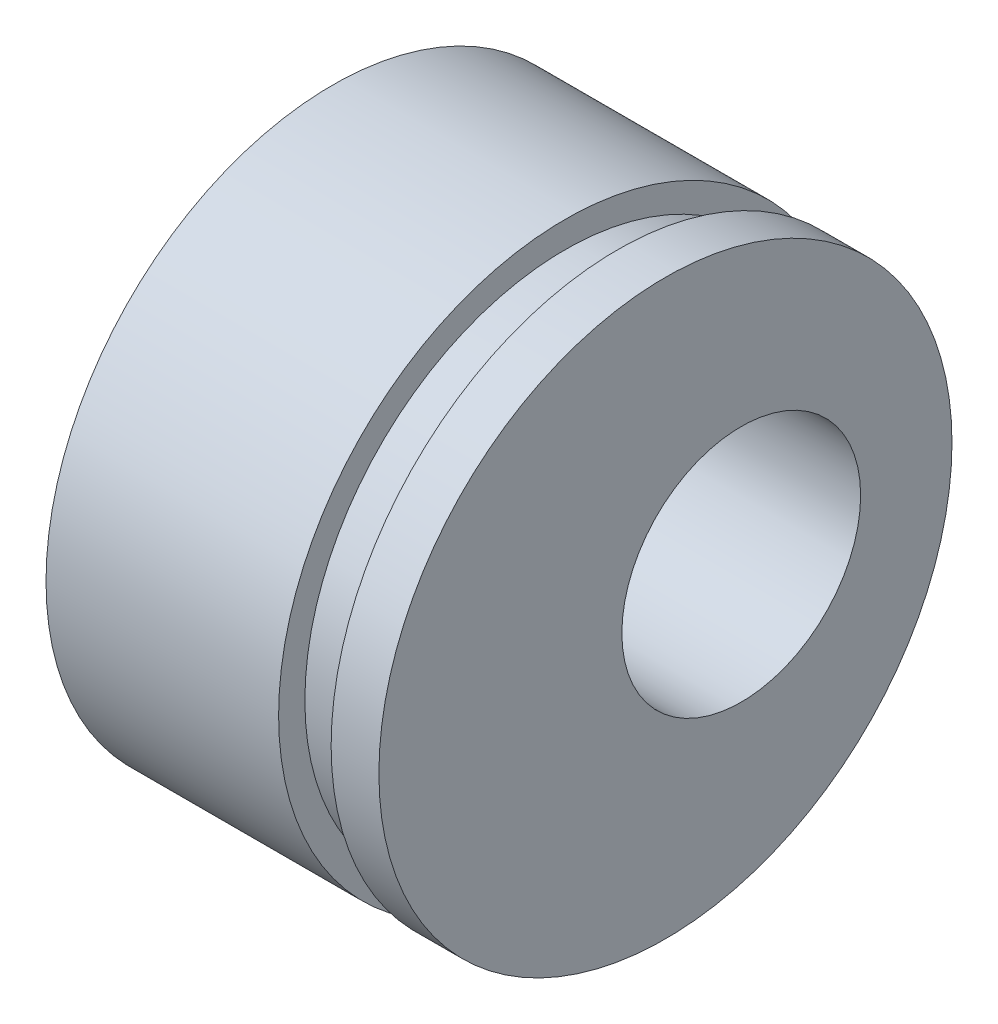
SolidWorks part; units mm, degrees
ref_plane "Front Plane" through (0, 0, 0) normal (0, 0, 1) x (1, 0, 0)
ref_plane "Top Plane" through (0, 0, 0) normal (0, 1, 0) x (1, 0, 0)
ref_plane "Right Plane" through (0, 0, 0) normal (1, 0, 0) x (0, 0, -1)
sketch "Sketch2" plane through (0, 0, 0) normal (0, 0, 1) x (1, 0, 0)
  line L0 (0, 0) -> (58.591, 0) construction
  line L2 (0, 0) -> (18.4, 0)
  line L3 (0, 0) -> (0, 2.5)
  line L4 (0, 2.5) -> (18.4, 2.5)
  line L5 (18.4, 0) -> (18.4, 2.5)
  line L6 (6.0094, 2.5) -> (6.0094, 6)
  line L11 (6.0094, 6) -> (9.9794, 6)
  line L16 (12.9794, 6) -> (12.9794, 3)
  line L17 (12.9794, 3) -> (13.6398, 3)
  line L18 (13.6398, 3) -> (13.6398, 2.5)
  line L19 (13.6398, 2.5) -> (6.0094, 2.5)
  line L22 (13.6398, 2.5) -> (16.1198, 2.5)
  line L23 (13.6398, 2.5) -> (13.6398, 4)
  line L24 (13.6398, 4) -> (16.1198, 4)
  line L25 (16.1198, 2.5) -> (16.1198, 4)
  line L27 (6.0094, 6) -> (9.9794, 6)
  line L28 (6.0094, 6) -> (6.0094, 9)
  line L29 (6.0094, 9) -> (9.9794, 9)
  line L30 (9.9794, 6) -> (9.9794, 9)
  line L31 (6.0094, 9) -> (6.0094, 8.25)
  line L32 (6.0094, 8.25) -> (5.0094, 8.25)
  line L33 (8.6609, 22.001) -> (8.6609, 12.476) construction
  line L34 (5.0094, 12.476) -> (12.3124, 12.476)
  line L35 (9.9794, 9) -> (12.3124, 9)
  line L36 (5.0094, 7.9375) -> (1.7709, 7.9375)
  line L37 (5.0094, 8.25) -> (5.0094, 12.476)
  line L38 (5.0094, 7.9375) -> (5.0094, 13.9365)
  line L39 (5.0094, 13.9365) -> (1.7709, 13.9365)
  line L40 (1.7709, 7.9375) -> (1.7709, 13.9365)
  line L41 (5.0094, 22.001) -> (12.3124, 22.001)
  line L42 (5.0094, 22.001) -> (5.0094, 30.1625)
  line L43 (5.0094, 30.1625) -> (12.3124, 30.1625)
  line L44 (12.3124, 22.001) -> (12.3124, 30.1625)
  line L49 (16.6398, 22.001) -> (16.6398, 7.5)
  line L51 (23.0198, 7.5) -> (23.0198, 6.5)
  line L54 (16.1198, 4) -> (13.6398, 4)
  line L56 (18.0398, 7.5) -> (23.0198, 7.5)
  line L57 (13.3124, 22.001) -> (16.6398, 22.001)
  line L58 (16.1198, 3.5) -> (20.0198, 3.5)
  line L59 (29.9098, 14) -> (26.9098, 11)
  line L60 (4.0094, 31.75) -> (18.0398, 31.75)
  line L61 (18.0398, 7.5) -> (23.0198, 7.5)
  line L62 (18.0398, 7.5) -> (18.0398, 12)
  line L63 (18.0398, 12) -> (23.0198, 12)
  line L64 (23.0198, 7.5) -> (23.0198, 12)
  line L65 (18.0398, 31.75) -> (18.0398, 12)
  line L66 (23.0198, 11) -> (26.9098, 11)
  line L67 (34.8098, 23) -> (31.3098, 19.5)
  line L68 (35.8098, 31) -> (38.7998, 33.99)
  line L69 (29.9098, 14) -> (29.9098, 15)
  line L70 (29.9098, 15) -> (22.9398, 15)
  line L71 (22.9398, 15) -> (21.0398, 15)
  line L72 (18.0398, 7.5) -> (16.6398, 7.5)
  line L73 (21.0398, 15) -> (21.0398, 43)
  line L74 (19.6115, 40) -> (9.6516, 40)
  line L75 (9.6516, 40) -> (4.0094, 40)
  line L76 (21.0398, 43) -> (19.6115, 43)
  line L77 (22.9398, 15) -> (29.9098, 15)
  line L78 (22.9398, 15) -> (22.9398, 21)
  line L79 (22.9398, 21) -> (29.9098, 21)
  line L80 (29.9098, 15) -> (29.9098, 21)
  line L81 (9.6516, 40) -> (19.6115, 40)
  line L82 (9.6516, 40) -> (9.6516, 50)
  line L83 (9.6516, 50) -> (19.6115, 50)
  line L84 (19.6115, 40) -> (19.6115, 50)
  line L85 (4.0094, 40) -> (4.0094, 31.75)
  line L86 (12.9794, 3) -> (12.9794, 2.5)
  line L87 (31.3098, 19.5) -> (29.9098, 19.5)
  line L88 (21.4694, 63.5) -> (21.4694, 51.308)
  line L89 (21.4694, 63.5) -> (25.9398, 63.5)
  line L90 (25.9398, 63.5) -> (25.9398, 25)
  line L91 (27.8398, 25) -> (25.9398, 25)
  line L92 (9.6516, 48) -> (8.2233, 48)
  line L93 (8.2233, 48) -> (8.2233, 53.476)
  line L94 (8.2233, 53.476) -> (19.6115, 53.476)
  line L95 (19.6115, 53.476) -> (19.6115, 50)
  line L96 (13.9174, 63.001) -> (13.9174, 53.476) construction
  line L97 (8.2233, 63.001) -> (19.6115, 63.001)
  line L98 (8.2233, 63.001) -> (8.2233, 68.2625)
  line L99 (8.2233, 68.2625) -> (19.6115, 68.2625)
  line L100 (19.6115, 63.001) -> (19.6115, 68.2625)
  line L101 (12.9794, 6) -> (11.9794, 6)
  line L102 (8.2233, 44.825) -> (4.9848, 44.825)
  line L103 (8.2233, 44.825) -> (8.2233, 54.9365)
  line L104 (8.2233, 54.9365) -> (4.9848, 54.9365)
  line L106 (9.9794, 6) -> (10.8794, 6)
  line L107 (27.8398, 25) -> (34.8098, 25)
  line L108 (34.8098, 25) -> (34.8098, 23)
  line L109 (0, 0) -> (-2, 0)
  line L110 (0, 0) -> (0, 11)
  line L111 (27.8398, 25) -> (34.8098, 25)
  line L112 (27.8398, 25) -> (27.8398, 32.5)
  line L113 (27.8398, 32.5) -> (34.8098, 32.5)
  line L114 (34.8098, 25) -> (34.8098, 32.5)
  line L115 (35.8098, 31) -> (34.8098, 31)
  line L116 (27.8398, 32.5) -> (27.8398, 64.5)
  line L117 (20.5849, 74.025) -> (6.2499, 74.025)
  line L118 (6.2499, 74.025) -> (6.2499, 76.2)
  line L119 (38.7998, 47.29) -> (30.8398, 55.25)
  line L120 (0, 11) -> (-2, 11)
  line L121 (38.7998, 43.815) -> (30.8623, 43.815)
  line L123 (-4.8152, 69.85) -> (1.5348, 76.2)
  line L124 (38.7998, 47.29) -> (38.7998, 33.99)
  line L125 (-2, 0) -> (-2, 11)
  line L126 (38.7998, 37.465) -> (30.8623, 37.465)
  line L127 (30.8623, 43.815) -> (30.8623, 37.465)
  line L128 (6.0094, 2.5) -> (6.0094, 0)
  line L129 (-0.0152, 63.5) -> (-0.0152, 30)
  line L132 (4.9848, 63.5) -> (-0.0152, 63.5)
  line L136 (-1.8152, 30) -> (-11.7752, 30)
  line L138 (-13.7752, 25.4) -> (-2, 25.4)
  line L139 (-2, 25.4) -> (-2, 11.5)
  line L140 (27.8398, 64.5) -> (20.5849, 64.5)
  line L141 (-1.8152, 30) -> (-11.7752, 30)
  line L142 (-1.8152, 30) -> (-1.8152, 39)
  line L143 (-1.8152, 39) -> (-11.7752, 39)
  line L144 (-11.7752, 30) -> (-11.7752, 39)
  line L145 (20.5849, 64.5) -> (20.5849, 74.025)
  line L146 (-12.7752, 37) -> (-12.7752, 47.29)
  line L147 (-12.7752, 37) -> (-11.7752, 37)
  line L148 (30.8398, 55.25) -> (30.8398, 76.2)
  line L149 (11.9794, 6) -> (11.9794, 5.45)
  line L154 (-2, 11.5) -> (0.5, 11.5)
  line L155 (4.9848, 60.6197) -> (24.0348, 60.6197)
  line L160 (4.9848, 60.6197) -> (4.9848, 55.8572)
  line L161 (4.9848, 55.8572) -> (24.0348, 55.8572)
  line L166 (24.0348, 60.6197) -> (24.0348, 55.8572)
  line L167 (4.9848, 60.6197) -> (24.0348, 55.8572) construction
  line L172 (4.9848, 55.8572) -> (24.0348, 60.6197) construction
  line L173 (24.0348, 62.2072) -> (25.9398, 62.2072)
  line L174 (11.9794, 5.45) -> (10.8794, 5.45)
  line L175 (10.8794, 6) -> (10.8794, 5.45)
  line L176 (24.0348, 62.2072) -> (24.0348, 54.2697)
  line L177 (24.0348, 54.2697) -> (25.9398, 54.2697)
  line L178 (25.9398, 62.2072) -> (25.9398, 54.2697)
  line L179 (24.0348, 62.2072) -> (25.9398, 54.2697) construction
  line L180 (24.0348, 54.2697) -> (25.9398, 62.2072) construction
  line L181 (3, 19.6197) -> (15.7, 19.6197)
  line L182 (3, 19.6197) -> (3, 14.8572)
  line L183 (3, 14.8572) -> (15.7, 14.8572)
  line L184 (15.7, 19.6197) -> (15.7, 14.8572)
  line L185 (3, 19.6197) -> (15.7, 14.8572) construction
  line L186 (3, 14.8572) -> (15.7, 19.6197) construction
  line L187 (15.7, 21.2072) -> (16.6398, 21.2072)
  line L188 (15.7, 21.2072) -> (15.7, 13.2697)
  line L189 (15.7, 13.2697) -> (16.6398, 13.2697)
  line L190 (16.6398, 21.2072) -> (16.6398, 13.2697)
  line L191 (15.7, 21.2072) -> (16.6398, 13.2697) construction
  line L192 (15.7, 13.2697) -> (16.6398, 21.2072) construction
  line L193 (0.5, 11.5) -> (0.5, 6.9375)
  line L194 (0.5, 6.9375) -> (1.7709, 6.9375)
  line L195 (23.0198, 6.5) -> (20.0198, 3.5)
  line L196 (4.9848, 63.5) -> (4.9848, 54.9365)
  line L197 (3, 43.825) -> (4.9848, 43.825)
  line L198 (1.7709, 6.9375) -> (1.7709, 7.9375)
  line L199 (6.0094, 0) -> (12.9794, 0)
  line L200 (12.9794, 0) -> (12.9794, 2.5)
  line L201 (18.0398, 31.75) -> (18.0398, 35.875)
  line L202 (18.0398, 35.875) -> (21.0398, 35.875)
  line L203 (30.8398, 76.2) -> (6.2499, 76.2)
  line L204 (2.8049, 69.85) -> (7.2499, 69.85) construction
  line L205 (7.2499, 67.4688) -> (26.2999, 67.4688)
  line L206 (7.2499, 74.025) -> (7.2499, 64.5)
  line L207 (7.2499, 64.5) -> (-1.8152, 64.5)
  line L208 (-1.8152, 64.5) -> (-1.8152, 39)
  line L209 (-12.7752, 47.29) -> (-4.8152, 55.25)
  line L210 (-4.8152, 55.25) -> (-4.8152, 69.85)
  line L211 (7.2499, 67.4688) -> (7.2499, 72.2312)
  line L212 (7.2499, 72.2312) -> (26.2999, 72.2313)
  line L213 (26.2999, 67.4688) -> (26.2999, 72.2313)
  line L214 (26.2999, 73.8187) -> (30.8398, 73.8187)
  line L215 (26.2999, 73.8187) -> (26.2999, 65.8813)
  line L216 (26.2999, 65.8813) -> (30.8398, 65.8813)
  line L217 (30.8398, 73.8187) -> (30.8398, 65.8813)
  line L218 (2.8049, 72.2313) -> (25.0299, 72.2313)
  line L219 (2.8049, 72.2313) -> (2.8049, 67.4687)
  line L220 (2.8049, 67.4687) -> (25.0299, 67.4687)
  line L221 (25.0299, 72.2313) -> (25.0299, 67.4687)
  line L222 (25.0299, 69.85) -> (20.5849, 69.85) construction
  line L223 (21.4694, 51.308) -> (22.9398, 51.308)
  line L224 (22.9398, 51.308) -> (22.9398, 21)
  line L225 (13.6398, 4) -> (13.6398, 12.2697)
  line L226 (13.6398, 12.2697) -> (13.3124, 12.2697)
  line L227 (13.3124, 12.2697) -> (13.3124, 22.001)
  line L228 (12.3124, 9) -> (12.3124, 12.476)
  line L229 (-1.8152, 30) -> (-0.0152, 30)
  line L230 (8.2233, 65.6317) -> (2.8049, 65.6317) construction
  line L231 (19.6115, 65.6317) -> (25.0299, 65.6317) construction
  line L232 (1.5348, 76.2) -> (6.2499, 76.2)
  line L233 (-11.7752, 30) -> (-13.7752, 30)
  line L234 (-13.7752, 30) -> (-13.7752, 25.4)
  line L235 (3, 13.9365) -> (3, 43.825)
  line L236 (4.9848, 54.9365) -> (4.9848, 44.825)
  line L237 (4.9848, 43.825) -> (4.9848, 44.825)
  circle A0 centre (26.8898, 25.95) radius 0.95
  circle A1 centre (21.9898, 15.95) radius 0.95
  circle A2 centre (17.3398, 8.2) radius 0.7
  circle A3 centre (10.4294, 6.45) radius 0.45
  circle A4 centre (-0.9152, 30.9) radius 0.9
  point P7 (24.9873, 58.2385)
  point P131 (16.1699, 17.2385)
  point P135 (14.5098, 58.2385)
  point P146 (9.35, 17.2385)
sketch "Sketch3" plane through (0, 0, 0) normal (0, 0, 1) x (1, 0, 0)
  line L0 (12.9794, 3) -> (12.9794, 2.5) construction
  line L1 (11.9794, 6) -> (11.9794, 5.45) construction
  line L2 (12.9794, 6) -> (11.9794, 6) construction
  line L3 (12.9794, 6) -> (12.9794, 3) construction
  line L5 (10.8794, 6) -> (10.8794, 5.45) construction
  line L6 (11.9794, 5.45) -> (10.8794, 5.45) construction
  line L7 (6.0094, 2.5) -> (6.0094, 6) construction
  line L8 (6.0094, 6) -> (9.9794, 6) construction
  line L9 (9.9794, 6) -> (10.8794, 6) construction
  line L10 (12.9794, 3) -> (12.9794, 2.5)
  line L11 (11.9794, 6) -> (11.9794, 5.45)
  line L12 (12.9794, 6) -> (11.9794, 6)
  line L13 (12.9794, 6) -> (12.9794, 3)
  line L15 (10.8794, 6) -> (10.8794, 5.45)
  line L16 (11.9794, 5.45) -> (10.8794, 5.45)
  line L17 (6.0094, 2.5) -> (6.0094, 6)
  line L18 (6.0094, 6) -> (9.9794, 6)
  line L19 (9.9794, 6) -> (10.8794, 6)
  line L20 (6.0094, 2.5) -> (6.0094, 0) construction
  line L21 (0, 0) -> (18.4, 0) construction
  line L22 (12.9794, 0) -> (12.9794, 2.5) construction
  line L23 (6.0094, 2.5) -> (6.0094, 0)
  line L24 (6.0094, 0) -> (12.9794, 0)
  line L25 (12.9794, 0) -> (12.9794, 2.5)
revolve "Revolve1" add sketch "Sketch3" angle 360 about L24
sketch "Sketch4" plane through (0, 0, 0) normal (1, 0, 0) x (0, 0, -1)
  line L0 (0, 0) -> (0, 69.85) construction
  line L1 (0, 0) -> (13.6271, 68.5079) construction
  line L2 (0, 0) -> (0, 58.2385) construction
  line L3 (0, 0) -> (50.436, 29.1192) construction
  line L4 (0, 0) -> (0, 31.75) construction
  line L5 (0, 0) -> (12.1502, 29.3332) construction
  line L6 (0, 0) -> (0, 17.2385) construction
  line L7 (0, 0) -> (14.929, 8.6192) construction
  line L8 (0, 0) -> (0, 58.2385) construction
  line L9 (0, 0) -> (50.436, 29.1192) construction
  line L10 (0, 0) -> (5.9583, 29.9542) construction
  line L11 (0, 0) -> (16.9677, 25.394) construction
  circle A0 centre (0, 0) radius 69.85 construction
  circle A1 centre (0, 0) radius 58.2385 construction
  circle A2 centre (0, 0) radius 31.75 construction
  circle A3 centre (0, 0) radius 17.2385 construction
  circle A4 centre (0, 69.85) radius 3.175
  circle A5 centre (0, 58.2385) radius 4.7625
  circle A6 centre (0, 31.75) radius 3.175
  circle A7 centre (0, 17.2385) radius 4.7625
  circle A8 centre (13.6271, 68.5079) radius 3.175
  circle A9 centre (26.7304, 64.533) radius 3.175
  circle A10 centre (38.8066, 58.0782) radius 3.175
  circle A11 centre (49.3914, 49.3914) radius 3.175
  circle A12 centre (58.0782, 38.8066) radius 3.175
  circle A13 centre (64.533, 26.7304) radius 3.175
  circle A14 centre (68.5079, 13.6271) radius 3.175
  circle A15 centre (69.85, 0) radius 3.175
  circle A16 centre (68.5079, -13.6271) radius 3.175
  circle A17 centre (64.533, -26.7304) radius 3.175
  circle A18 centre (58.0782, -38.8066) radius 3.175
  circle A19 centre (49.3914, -49.3914) radius 3.175
  circle A20 centre (38.8066, -58.0782) radius 3.175
  circle A21 centre (26.7304, -64.533) radius 3.175
  circle A22 centre (13.6271, -68.5079) radius 3.175
  circle A23 centre (0, -69.85) radius 3.175
  circle A24 centre (-13.6271, -68.5079) radius 3.175
  circle A25 centre (-26.7304, -64.533) radius 3.175
  circle A26 centre (-38.8066, -58.0782) radius 3.175
  circle A27 centre (-49.3914, -49.3914) radius 3.175
  circle A28 centre (-58.0782, -38.8066) radius 3.175
  circle A29 centre (-64.533, -26.7304) radius 3.175
  circle A30 centre (-68.5079, -13.6271) radius 3.175
  circle A31 centre (-69.85, 0) radius 3.175
  circle A32 centre (-68.5079, 13.6271) radius 3.175
  circle A33 centre (-64.533, 26.7304) radius 3.175
  circle A34 centre (-58.0782, 38.8066) radius 3.175
  circle A35 centre (-49.3914, 49.3914) radius 3.175
  circle A36 centre (-38.8066, 58.0782) radius 3.175
  circle A37 centre (-26.7304, 64.533) radius 3.175
  circle A38 centre (-13.6271, 68.5079) radius 3.175
  circle A47 centre (50.436, 29.1192) radius 4.7625
  circle A48 centre (50.436, -29.1192) radius 4.7625
  circle A49 centre (0, -58.2385) radius 4.7625
  circle A50 centre (-50.436, -29.1192) radius 4.7625
  circle A51 centre (-50.436, 29.1192) radius 4.7625
  circle A58 centre (12.1502, 29.3332) radius 3.175
  circle A59 centre (22.4506, 22.4506) radius 3.175
  circle A60 centre (29.3332, 12.1502) radius 3.175
  circle A61 centre (31.75, 0) radius 3.175
  circle A62 centre (29.3332, -12.1502) radius 3.175
  circle A63 centre (22.4506, -22.4506) radius 3.175
  circle A64 centre (12.1502, -29.3332) radius 3.175
  circle A65 centre (0, -31.75) radius 3.175
  circle A66 centre (-12.1502, -29.3332) radius 3.175
  circle A67 centre (-22.4506, -22.4506) radius 3.175
  circle A68 centre (-29.3332, -12.1502) radius 3.175
  circle A69 centre (-31.75, 0) radius 3.175
  circle A70 centre (-29.3332, 12.1502) radius 3.175
  circle A71 centre (-22.4506, 22.4506) radius 3.175
  circle A72 centre (14.929, 8.6192) radius 4.7625
  circle A73 centre (14.929, -8.6192) radius 4.7625
  circle A74 centre (0, -17.2385) radius 4.7625
  circle A75 centre (-14.929, -8.6192) radius 4.7625
  circle A76 centre (-14.929, 8.6192) radius 4.7625
  circle A77 centre (0, 0) radius 50
  circle A78 centre (0, 0) radius 9
  circle A79 centre (-12.1502, 29.3332) radius 3.175
  circle A80 centre (0, 0) radius 76.2
  circle A81 centre (0, 0) radius 74.025
  circle A82 centre (0, 69.85) radius 3.9687
  circle A83 centre (49.3914, 49.3914) radius 3.9687
  circle A84 centre (69.85, 0) radius 3.9688
  circle A85 centre (49.3914, -49.3914) radius 3.9687
  circle A86 centre (0, -69.85) radius 3.9687
  circle A87 centre (-49.3914, -49.3914) radius 3.9687
  circle A88 centre (-69.85, 0) radius 3.9688
  circle A89 centre (-49.3914, 49.3914) radius 3.9687
  circle A90 centre (0, 69.85) radius 2.3812
  circle A91 centre (13.6271, 68.5079) radius 2.3812
  circle A92 centre (26.7304, 64.533) radius 2.3813
  circle A93 centre (38.8066, 58.0782) radius 2.3812
  circle A94 centre (49.3914, 49.3914) radius 2.3812
  circle A95 centre (58.0782, 38.8066) radius 2.3812
  circle A96 centre (64.533, 26.7304) radius 2.3813
  circle A97 centre (68.5079, 13.6271) radius 2.3813
  circle A98 centre (69.85, 0) radius 2.3813
  circle A99 centre (68.5079, -13.6271) radius 2.3813
  circle A100 centre (64.533, -26.7304) radius 2.3813
  circle A101 centre (58.0782, -38.8066) radius 2.3812
  circle A102 centre (49.3914, -49.3914) radius 2.3812
  circle A103 centre (38.8066, -58.0782) radius 2.3812
  circle A104 centre (26.7304, -64.533) radius 2.3813
  circle A105 centre (13.6271, -68.5079) radius 2.3812
  circle A106 centre (0, -69.85) radius 2.3812
  circle A107 centre (-13.6271, -68.5079) radius 2.3812
  circle A108 centre (-26.7304, -64.533) radius 2.3813
  circle A109 centre (-38.8066, -58.0782) radius 2.3812
  circle A110 centre (-49.3914, -49.3914) radius 2.3812
  circle A111 centre (-58.0782, -38.8066) radius 2.3812
  circle A112 centre (-64.533, -26.7304) radius 2.3812
  arc A113 (3.0399, 30.8338) -> (8.9911, 29.65) centre (5.9583, 29.9542) cw
  arc A114 (14.6081, 27.3234) -> (19.6532, 23.9523) centre (16.9677, 25.394) cw
  arc A115 (23.9523, 19.6532) -> (27.3234, 14.6081) centre (25.394, 16.9677) cw
  arc A116 (29.65, 8.9911) -> (30.8338, 3.0399) centre (29.9542, 5.9583) cw
  arc A117 (30.8338, -3.0399) -> (29.65, -8.9911) centre (29.9542, -5.9583) cw
  arc A118 (27.3234, -14.6081) -> (23.9523, -19.6532) centre (25.394, -16.9677) cw
  arc A119 (19.6532, -23.9523) -> (14.6081, -27.3234) centre (16.9677, -25.394) cw
  arc A120 (8.9911, -29.65) -> (3.0399, -30.8338) centre (5.9583, -29.9542) cw
  arc A121 (-3.0399, -30.8338) -> (-8.9911, -29.65) centre (-5.9583, -29.9542) cw
  arc A122 (-14.6081, -27.3234) -> (-19.6532, -23.9523) centre (-16.9677, -25.394) cw
  arc A123 (-23.9523, -19.6532) -> (-27.3234, -14.6081) centre (-25.394, -16.9677) cw
  arc A124 (-29.65, -8.9911) -> (-30.8338, -3.0399) centre (-29.9542, -5.9583) cw
  arc A125 (-30.8338, 3.0399) -> (-29.65, 8.9911) centre (-29.9542, 5.9583) cw
  arc A126 (-27.3234, 14.6081) -> (-23.9523, 19.6532) centre (-25.394, 16.9677) cw
  arc A127 (-19.6532, 23.9523) -> (-14.6081, 27.3234) centre (-16.9677, 25.394) cw
  arc A128 (-8.9911, 29.65) -> (-3.0399, 30.8338) centre (-5.9583, 29.9542) cw
  arc A129 (26.9875, 0) -> (26.9932, 0.1932) centre (30.2705, 0) cw
  arc A130 (65.0988, 0.2771) -> (65.0875, 0) centre (68.4964, 0) ccw
  circle A131 centre (1.5875, 0) radius 40
  circle A132 centre (1.5875, 0) radius 2.5
  circle A133 centre (1.5875, 0) radius 3
  circle A134 centre (1.5875, 0) radius 43
  circle A135 centre (-68.5079, -13.6271) radius 2.3813
  circle A136 centre (-69.85, 0) radius 2.3813
  circle A137 centre (-68.5079, 13.6271) radius 2.3813
  circle A138 centre (-64.533, 26.7304) radius 2.3812
  circle A139 centre (-58.0782, 38.8066) radius 2.3812
  circle A140 centre (-49.3914, 49.3914) radius 2.3812
  circle A141 centre (-38.8066, 58.0782) radius 2.3812
  circle A142 centre (-26.7304, 64.533) radius 2.3813
  circle A143 centre (-13.6271, 68.5079) radius 2.3812
  circle A144 centre (0, 58.2385) radius 2.3812
  circle A145 centre (0, 58.2385) radius 3.9688
  circle A146 centre (50.436, 29.1192) radius 3.9688
  circle A147 centre (50.436, 29.1192) radius 2.3813
  circle A148 centre (50.436, -29.1192) radius 3.9687
  circle A149 centre (50.436, -29.1192) radius 2.3812
  circle A150 centre (0, -58.2385) radius 3.9687
  circle A151 centre (0, -58.2385) radius 2.3812
  circle A152 centre (-50.436, -29.1192) radius 3.9687
  circle A153 centre (-50.436, -29.1192) radius 2.3812
  circle A154 centre (-50.436, 29.1192) radius 3.9687
  circle A155 centre (-50.436, 29.1192) radius 2.3812
  spline S1 degree 4 poles (26.9875, 0) (26.9875, -0.0248) (26.9882, -0.0743) (26.9912, -0.1613) (26.9992, -0.2849) (27.0142, -0.4323) (27.0403, -0.5994) (27.0821, -0.7965) (27.1455, -1.0177) (27.2241, -1.2336) (27.3173, -1.4437) (27.4329, -1.6623) (27.5739, -1.8864) (27.7427, -2.1125) (27.9417, -2.3365) (28.1305, -2.5184) (28.3007, -2.6647) (28.4457, -2.7828) (28.5617, -2.8775) (28.6745, -2.9758) (28.7813, -3.0807) (28.9057, -3.2206) (29.0482, -3.4108) (29.197, -3.6576) (29.3758, -4.0447) (29.5291, -4.5502) (29.6152, -5.1612) (29.5933, -5.8758) (29.4507, -6.5869) (29.186, -7.2733) (28.8461, -7.831) (28.4818, -8.2549) (28.1375, -8.5536) (27.8792, -8.7284) (27.6484, -8.8496) (27.4154, -8.9438) (27.2144, -9.0029) (27.0118, -9.0554) (26.7709, -9.1263) (26.5334, -9.2082) (26.2634, -9.3231) (25.9685, -9.4827) (25.5538, -9.7623) (25.0678, -10.2216) (24.6281, -10.8948) (24.3613, -11.7878) (24.3459, -12.6097) (24.4764, -13.2366) (24.6525, -13.7006) (24.8058, -14.0202) (24.9382, -14.271) (25.0503, -14.5321) (25.1258, -14.8064) (25.1736, -15.0995) (25.1911, -15.4094) (25.1742, -15.8163) (25.0891, -16.3148) (24.907, -16.8764) (24.5182, -17.6315) (23.9757, -18.2942) (23.3695, -18.7764) (22.7564, -19.084) (22.3641, -19.2199) (22.0554, -19.2923) (21.7533, -19.3289) (21.4612, -19.3296) (21.1723, -19.2896) (20.8852, -19.2417) (20.5956, -19.2104) (20.3043, -19.1994) (19.8669, -19.2177) (19.2899, -19.3231) (18.5833, -19.6092) (17.8444, -20.1834) (17.3807, -20.828) (17.1316, -21.424) (17.0182, -21.8879) (16.9714, -22.1971) (16.9537, -22.4701) (16.9533, -22.7044) (16.9619, -22.9384) (16.9737, -23.1333) (16.977, -23.3286) (16.9594, -23.5624) (16.9177, -23.8101) (16.834, -24.1055) (16.6578, -24.5276) (16.3623, -25.0151) (15.9278, -25.5198) (15.3432, -25.99) (14.6957, -26.3472) (14.0068, -26.5857) (13.3856, -26.6851) (12.847, -26.6849) (12.4166, -26.6224) (12.1324, -26.5468) (11.9058, -26.4598) (11.7342, -26.3753) (11.6017, -26.2989) (11.4727, -26.2169) (11.3444, -26.1337) (11.1825, -26.0322) (10.9836, -25.9179) (10.7435, -25.7991) (10.4587, -25.6867) (10.0106, -25.5536) (9.3843, -25.468) (8.599, -25.5363) (7.7243, -25.8773) (7.1093, -26.3459) (6.716, -26.8042) (6.4745, -27.1841) (6.3352, -27.4489) (6.215, -27.7227) (6.1113, -28.0028) (5.9959, -28.2789) (5.841, -28.5357) (5.6522, -28.7792) (5.4316, -29.007) (5.1188, -29.2711) (4.6965, -29.5439) (4.1624, -29.7882) (3.5487, -29.9564) (2.9521, -30.0296) (2.386, -30.0225) (1.8595, -29.949) (1.3409, -29.8055) (0.9058, -29.6147) (0.5544, -29.4004) (0.2828, -29.1832) (0.0847, -28.9875) (-0.0865, -28.768) (-0.2353, -28.5332) (-0.3904, -28.3016) (-0.5598, -28.0786) (-0.792, -27.8146) (-1.1036, -27.5274) (-1.5105, -27.2448) (-2.0688, -26.9834) (-2.7167, -26.8202) (-3.459, -26.7949) (-4.1529, -26.9407) (-4.7224, -27.1899) (-5.1296, -27.455) (-5.3866, -27.661) (-5.5925, -27.8507) (-5.7558, -28.014) (-5.9199, -28.1766) (-6.0977, -28.3246) (-6.3382, -28.4851) (-6.6906, -28.6628) (-7.1669, -28.8182) (-7.7668, -28.9076) (-8.4201, -28.8957) (-9.0747, -28.7804) (-9.7144, -28.5614) (-10.3217, -28.2381) (-10.8061, -27.8636) (-11.1671, -27.4837) (-11.4143, -27.1402) (-11.5734, -26.859) (-11.6946, -26.573) (-11.7735, -26.2857) (-11.8173, -25.9915) (-11.8668, -25.6988) (-11.9353, -25.4093) (-12.0257, -25.1261) (-12.198, -24.7091) (-12.5089, -24.187) (-13.0379, -23.6191) (-13.8448, -23.1355) (-14.6072, -22.9365) (-15.2369, -22.9149) (-15.701, -22.9694) (-16.0024, -23.0316) (-16.2609, -23.107) (-16.4782, -23.1841) (-16.6576, -23.2529) (-16.8015, -23.307) (-16.9839, -23.3672) (-17.2087, -23.4203) (-17.4853, -23.4534) (-17.811, -23.4543) (-18.2291, -23.4104) (-18.7305, -23.2885) (-19.2884, -23.06) (-19.8603, -22.7052) (-20.3581, -22.2764) (-20.7758, -21.7899) (-21.1086, -21.2598) (-21.3336, -20.7318) (-21.4619, -20.2263) (-21.5006, -19.8113) (-21.4889, -19.4989) (-21.4468, -19.2424) (-21.3965, -19.0408) (-21.34, -18.8332) (-21.2878, -18.6168) (-21.2341, -18.3322) (-21.1962, -17.9773) (-21.1985, -17.5604) (-21.2781, -17.0173) (-21.4721, -16.4256) (-21.838, -15.7861) (-22.3482, -15.2578) (-22.8946, -14.8957) (-23.3828, -14.6878) (-23.7368, -14.5834) (-24.0536, -14.5215) (-24.3285, -14.4876) (-24.6045, -14.47) (-24.8811, -14.458) (-25.1556, -14.4184) (-25.4228, -14.3439) (-25.6932, -14.2375) (-26.1109, -14.0218) (-26.5677, -13.6822) (-27.0258, -13.1981) (-27.4314, -12.5682) (-27.7017, -11.9578) (-27.8746, -11.3112) (-27.9332, -10.727) (-27.9111, -10.2247) (-27.8415, -9.8214) (-27.7568, -9.5159) (-27.6427, -9.2298) (-27.5004, -8.9659) (-27.3212, -8.7261) (-27.1301, -8.4966) (-26.9071, -8.1967) (-26.6417, -7.7583) (-26.3997, -7.1508) (-26.2841, -6.3875) (-26.3642, -5.5798) (-26.6019, -4.9055) (-26.9193, -4.3761) (-27.2736, -3.9636) (-27.583, -3.6904) (-27.8719, -3.4871) (-28.1186, -3.3407) (-28.3135, -3.2371) (-28.5043, -3.1411) (-28.6854, -3.0419) (-28.9002, -2.8984) (-29.1355, -2.6958) (-29.4123, -2.3882) (-29.6958, -1.9552) (-29.932, -1.437) (-30.0985, -0.839) (-30.1779, -0.2025) (-30.1603, 0.4599) (-30.0348, 1.1323) (-29.8199, 1.711) (-29.5617, 2.1719) (-29.3035, 2.5118) (-29.0784, 2.748) (-28.8655, 2.924) (-28.6761, 3.0468) (-28.5112, 3.1367) (-28.3775, 3.205) (-28.2106, 3.2911) (-28.0136, 3.4005) (-27.7912, 3.5413) (-27.5508, 3.7219) (-27.2011, 4.0343) (-26.7941, 4.5285) (-26.4419, 5.234) (-26.2777, 6.1494) (-26.351, 6.9081) (-26.5268, 7.4739) (-26.7218, 7.8823) (-26.8619, 8.1196) (-26.9953, 8.3144) (-27.1373, 8.5028) (-27.2613, 8.6553) (-27.3845, 8.8088) (-27.518, 9.0035) (-27.6324, 9.2103) (-27.7412, 9.4693) (-27.8326, 9.7814) (-27.9074, 10.1885) (-27.9345, 10.6913) (-27.8808, 11.2771) (-27.6878, 12.0229) (-27.3166, 12.8111) (-26.8405, 13.4278) (-26.3243, 13.8718) (-25.9118, 14.1263) (-25.6503, 14.2566) (-25.3769, 14.3596) (-25.0933, 14.4318) (-24.8027, 14.4634) (-24.5112, 14.4738) (-24.1629, 14.5033) (-23.7608, 14.5717) (-23.1887, 14.7443) (-22.5511, 15.0901) (-21.962, 15.6231) (-21.544, 16.2749) (-21.3217, 16.857) (-21.2175, 17.3851) (-21.1902, 17.8397) (-21.2185, 18.2374) (-21.2771, 18.5739) (-21.3443, 18.8506) (-21.405, 19.0706) (-21.4579, 19.2928) (-21.4883, 19.5194) (-21.4981, 19.805) (-21.4664, 20.1907) (-21.3565, 20.6672) (-21.1331, 21.2135) (-20.8025, 21.7541) (-20.3882, 22.2461) (-19.8974, 22.677) (-19.3379, 23.033) (-18.7964, 23.2649) (-18.309, 23.3941) (-17.8981, 23.4483) (-17.5726, 23.4572) (-17.2924, 23.4331) (-17.0602, 23.3874) (-16.8337, 23.3199) (-16.6495, 23.2499) (-16.4659, 23.1791) (-16.2424, 23.1025) (-16.0156, 23.0362) (-15.7461, 22.9768) (-15.2967, 22.9185) (-14.7035, 22.9278) (-13.9592, 23.0948) (-13.1407, 23.5365) (-12.5805, 24.0908) (-12.2382, 24.6309) (-12.0505, 25.0599) (-11.9538, 25.3442) (-11.8892, 25.5989) (-11.8463, 25.8198) (-11.8162, 26.0048) (-11.7926, 26.153) (-11.7577, 26.3372) (-11.6989, 26.5548) (-11.5969, 26.8111) (-11.4414, 27.0975) (-11.1977, 27.4473) (-10.8392, 27.8343) (-10.3554, 28.2166) (-9.7549, 28.5431) (-9.1303, 28.7642) (-8.5, 28.8851) (-7.879, 28.911) (-7.3126, 28.8458) (-6.8128, 28.7091) (-6.4345, 28.54) (-6.1692, 28.378) (-5.9665, 28.2173) (-5.8163, 28.0752) (-5.6659, 27.9232) (-5.5067, 27.7699) (-5.2907, 27.5806) (-5.0072, 27.369) (-4.6509, 27.1597) (-4.148, 26.9513) (-3.5452, 26.8146) (-2.8302, 26.7991) (-2.0381, 26.9749) (-1.3495, 27.3225) (-0.8483, 27.741) (-0.5146, 28.1291) (-0.2991, 28.4338) (-0.1401, 28.6862) (0.0331, 28.93) (0.2405, 29.146) (0.4774, 29.3422) (0.7418, 29.5165) (1.1036, 29.7066) (1.5741, 29.882) (2.1471, 30.006) (2.8151, 30.041) (3.4791, 29.9721) (4.2039, 29.7804) (4.8064, 29.4933) (5.2708, 29.1628) (5.6049, 28.8311) (5.7894, 28.6062) (5.9424, 28.3744) (6.0642, 28.1249) (6.161, 27.8653) (6.2635, 27.608) (6.3813, 27.357) (6.5388, 27.0748) (6.7484, 26.7704) (7.0986, 26.3707) (7.6135, 25.9641) (8.2747, 25.644) (8.9962, 25.4959) (9.6181, 25.496) (10.1582, 25.5894) (10.5546, 25.7168) (10.8796, 25.8629) (11.1331, 26.0022) (11.3224, 26.1188) (11.5021, 26.2366) (11.6784, 26.3463) (11.9094, 26.4649) (12.2028, 26.5718) (12.6092, 26.6624) (13.1291, 26.6958) (13.7, 26.6444) (14.3062, 26.4914) (14.8974, 26.2443) (15.459, 25.9029) (15.9732, 25.4681) (16.3631, 25.0071) (16.6337, 24.567) (16.8044, 24.1822) (16.9036, 23.8716) (16.9571, 23.5978) (16.9755, 23.3672) (16.9741, 23.1748) (16.9669, 23.0211) (16.9571, 22.8289) (16.9512, 22.5982) (16.9599, 22.3287) (16.9946, 22.0224) (17.0874, 21.5638) (17.3043, 20.9714) (17.7315, 20.3087) (18.4426, 19.693) (19.1468, 19.3677) (19.739, 19.2351) (20.1882, 19.2012) (20.4852, 19.2034) (20.7812, 19.2282) (21.0745, 19.2719) (21.3675, 19.3208) (21.6648, 19.3336) (21.9737, 19.306) (22.2899, 19.241) (22.6922, 19.1116) (23.1641, 18.8854) (23.669, 18.5404) (24.1634, 18.0628) (24.569, 17.5219) (24.8807, 16.9345) (25.0937, 16.316) (25.184, 15.7743) (25.1924, 15.3317) (25.1581, 14.9969) (25.1154, 14.7695) (25.0522, 14.5468) (24.9658, 14.3321) (24.8616, 14.1257) (24.7568, 13.9198) (24.6402, 13.6649) (24.524, 13.3562) (24.3985, 12.886) (24.3389, 12.2663) (24.4166, 11.5605) (24.6979, 10.7931) (25.0952, 10.2042) (25.5426, 9.7706) (25.9551, 9.4883) (26.2689, 9.3208) (26.5627, 9.1971) (26.83, 9.1062) (27.1019, 9.0315) (27.3749, 8.9598) (27.6385, 8.8574) (27.887, 8.7225) (28.1969, 8.5098) (28.5449, 8.1936) (28.9002, 7.7549) (29.2229, 7.1817) (29.4529, 6.562) (29.5858, 5.9108) (29.6165, 5.2432) (29.5485, 4.659) (29.4188, 4.1725) (29.2636, 3.7931) (29.1144, 3.5129) (28.9404, 3.2582) (28.7432, 3.0317) (28.5155, 2.8371) (28.281, 2.6515) (28.0578, 2.4519) (27.8492, 2.2371) (27.6347, 1.9761) (27.4574, 1.7102) (27.3152, 1.4444) (27.2047, 1.1845) (27.1307, 0.9703) (27.0789, 0.7793) (27.0441, 0.6164) (27.021, 0.472) (27.0061, 0.351) (26.9981, 0.2662) (26.9946, 0.2176) (26.9932, 0.1932) knots 0.06864 0.06864 0.06864 0.06864 0.06864 0.069106 0.069571 0.070037 0.070502 0.071433 0.072364 0.073295 0.074226 0.075157 0.076088 0.077301 0.078514 0.079727 0.08094 0.081547 0.082153 0.08276 0.083366 0.083973 0.084579 0.085792 0.087214 0.088636 0.091479 0.094323 0.097166 0.100174 0.103182 0.10619 0.107694 0.109198 0.110555 0.111234 0.111912 0.113269 0.113948 0.114626 0.115983 0.11734 0.118697 0.120055 0.12408 0.128106 0.131537 0.134967 0.137266 0.138415 0.139565 0.140714 0.141863 0.143013 0.144162 0.145524 0.146885 0.149608 0.152331 0.155054 0.160594 0.163364 0.164749 0.166134 0.167314 0.168495 0.169675 0.170855 0.172035 0.173215 0.174395 0.175575 0.179125 0.182676 0.186612 0.190548 0.191813 0.193079 0.194345 0.195611 0.196244 0.196877 0.198142 0.198775 0.199408 0.200674 0.202207 0.203741 0.206808 0.209874 0.212941 0.21584 0.218738 0.221637 0.223086 0.224535 0.225775 0.226394 0.227014 0.227634 0.228253 0.228873 0.229493 0.230732 0.231971 0.233211 0.23445 0.238303 0.242155 0.245814 0.249472 0.250683 0.251894 0.253105 0.254316 0.255527 0.256738 0.257949 0.25916 0.260514 0.261868 0.264577 0.267285 0.269993 0.272142 0.27429 0.276439 0.278588 0.280839 0.281965 0.283091 0.284217 0.285343 0.286469 0.287595 0.288737 0.289879 0.292163 0.294447 0.296732 0.299827 0.302922 0.306383 0.308113 0.309844 0.31078 0.311716 0.312652 0.313588 0.314524 0.31546 0.317332 0.319969 0.322606 0.325244 0.327881 0.330703 0.333524 0.336346 0.337757 0.339168 0.340372 0.341576 0.34278 0.343984 0.345188 0.346392 0.347596 0.3488 0.352495 0.356189 0.36002 0.36385 0.365096 0.366342 0.367588 0.368834 0.369457 0.370079 0.370702 0.371325 0.372571 0.373817 0.375207 0.376596 0.379375 0.382154 0.384933 0.387459 0.389986 0.392513 0.39504 0.396723 0.398407 0.399249 0.400091 0.400932 0.401774 0.402737 0.4037 0.405625 0.407551 0.409476 0.412569 0.415662 0.41939 0.421254 0.423119 0.42424 0.425361 0.426483 0.427604 0.428726 0.429847 0.430969 0.43209 0.433431 0.437455 0.440138 0.44282 0.445528 0.448236 0.450943 0.452297 0.453651 0.454862 0.456073 0.457284 0.458495 0.459706 0.460916 0.463338 0.466783 0.470228 0.473297 0.476366 0.478273 0.480179 0.482085 0.483038 0.483991 0.484828 0.485664 0.486501 0.487337 0.48901 0.490683 0.493189 0.495695 0.498202 0.500708 0.503552 0.506397 0.509241 0.510663 0.512085 0.513303 0.514521 0.51513 0.515738 0.516347 0.516956 0.518174 0.519391 0.520609 0.521827 0.525766 0.529706 0.533208 0.53671 0.537985 0.53926 0.540535 0.541173 0.54181 0.543085 0.543723 0.54436 0.545635 0.54691 0.548267 0.549623 0.552335 0.555047 0.55776 0.562061 0.566363 0.567545 0.568728 0.56991 0.571092 0.572275 0.573457 0.574639 0.575822 0.577939 0.580057 0.584292 0.587472 0.590653 0.592493 0.594334 0.596174 0.598014 0.59894 0.599865 0.60079 0.601715 0.60264 0.603565 0.605415 0.607973 0.610531 0.61309 0.615648 0.618364 0.62108 0.623796 0.625154 0.626512 0.627788 0.629065 0.629703 0.630341 0.631618 0.632256 0.632895 0.634171 0.635448 0.636724 0.640232 0.643739 0.647674 0.651609 0.652825 0.65404 0.655256 0.656472 0.65708 0.657688 0.658296 0.658904 0.66012 0.661336 0.662756 0.664177 0.667018 0.669858 0.672699 0.675209 0.677718 0.680227 0.682736 0.684412 0.686087 0.686924 0.687762 0.688599 0.689437 0.690391 0.691345 0.693254 0.695162 0.697071 0.700143 0.703216 0.706655 0.710095 0.712514 0.713723 0.714933 0.716142 0.717352 0.718561 0.719771 0.721123 0.722475 0.725179 0.727883 0.730587 0.733273 0.735959 0.739989 0.741332 0.742455 0.743577 0.7447 0.745823 0.746945 0.748068 0.749191 0.750314 0.752181 0.754048 0.757782 0.760871 0.763961 0.765883 0.767806 0.769729 0.77069 0.771651 0.772492 0.773333 0.774174 0.775015 0.776698 0.77838 0.780903 0.783427 0.785951 0.788475 0.791257 0.794039 0.796822 0.798213 0.799604 0.800852 0.802099 0.802723 0.803347 0.803971 0.804595 0.805842 0.80709 0.808337 0.809585 0.81342 0.817255 0.820945 0.824634 0.825837 0.827039 0.828242 0.829444 0.830647 0.831849 0.833052 0.834254 0.835663 0.837072 0.83989 0.842708 0.845526 0.848167 0.850807 0.853447 0.856087 0.857024 0.857961 0.858897 0.859834 0.860771 0.861707 0.862644 0.863581 0.865314 0.867048 0.870515 0.873613 0.876711 0.880181 0.881916 0.883651 0.884794 0.885937 0.887081 0.888224 0.889367 0.89051 0.891653 0.892797 0.895451 0.898105 0.90076 0.903414 0.906126 0.908838 0.911549 0.912905 0.914261 0.915474 0.916686 0.917899 0.919111 0.920323 0.921536 0.922748 0.923961 0.925793 0.926709 0.927625 0.928541 0.929457 0.929915 0.930373 0.930831 0.931289 0.931289 0.931289 0.931289 0.931289
  spline S3 degree 4 poles (65.0875, 0) (65.0875, -0.2085) (65.1336, -0.6093) (65.3196, -1.4523) (65.739, -2.0447) (66.242, -2.6341) (66.7299, -3.0916) (67.1731, -3.6257) (67.5219, -4.2566) (67.8399, -5.1354) (68.0042, -6.2629) (67.9043, -7.3956) (67.5534, -8.464) (67.1166, -9.2437) (66.7001, -9.7852) (66.2223, -10.2316) (65.7042, -10.5824) (65.1033, -10.9671) (64.5015, -11.4984) (63.9836, -12.2541) (63.7076, -13.0981) (63.6577, -13.8665) (63.7509, -14.5541) (63.9279, -15.1344) (64.2231, -15.7099) (64.6171, -16.2749) (64.9859, -16.8848) (65.2405, -17.5795) (65.3772, -18.3315) (65.3953, -19.1188) (65.2888, -19.9454) (65.0416, -20.7887) (64.6379, -21.6235) (64.0595, -22.4019) (63.3699, -23.0372) (62.5888, -23.4701) (61.782, -23.7464) (61.0578, -24.1183) (60.3658, -24.7064) (59.8816, -25.4078) (59.6093, -26.1527) (59.5127, -26.9191) (59.5498, -27.5888) (59.7273, -28.2781) (60.0289, -28.9687) (60.2831, -29.7025) (60.3758, -30.5026) (60.3272, -31.328) (60.135, -32.1571) (59.8183, -32.9321) (59.3945, -33.6382) (58.8781, -34.2627) (58.2824, -34.7917) (57.6299, -35.2075) (56.9378, -35.4918) (56.2305, -35.6333) (55.5425, -35.7436) (54.9192, -35.9451) (54.3784, -36.2357) (53.8226, -36.6647) (53.3379, -37.2279) (52.9635, -37.9633) (52.7754, -38.8477) (52.8002, -39.6949) (52.9662, -40.4335) (53.0501, -41.0953) (53.0299, -41.6741) (52.9556, -42.1601) (52.7999, -42.7542) (52.5204, -43.4371) (52.0123, -44.2743) (51.2999, -45.0323) (50.5074, -45.5996) (49.6888, -45.9749) (49.0001, -46.1726) (48.294, -46.2386) (47.5903, -46.2021) (46.9326, -46.2102) (46.3301, -46.3235) (45.6752, -46.561) (45.0214, -46.9572) (44.4035, -47.5835) (43.9713, -48.3909) (43.7706, -49.1822) (43.7338, -49.9181) (43.7302, -50.5816) (43.6334, -51.2608) (43.4079, -51.9357) (42.9846, -52.7556) (42.2668, -53.6506) (41.3533, -54.3599) (40.3007, -54.8365) (39.3996, -55.0391) (38.7109, -55.0871) (38.0679, -55.0221) (37.4791, -54.8813) (36.7945, -54.7238) (35.9925, -54.6786) (35.0907, -54.8522) (34.2981, -55.2648) (33.7257, -55.7777) (33.3141, -56.326) (33.0345, -56.8561) (32.8392, -57.4643) (32.7053, -58.1318) (32.5057, -58.8072) (32.1692, -59.4564) (31.7161, -60.06) (31.1587, -60.6027) (30.4857, -61.0865) (29.6999, -61.483) (28.8088, -61.7584) (27.9539, -61.8544) (27.2176, -61.8147) (26.5366, -61.6724) (25.9236, -61.4387) (25.2656, -61.0978) (24.4787, -60.8476) (23.5806, -60.7805) (22.7614, -60.9343) (22.0678, -61.2531) (21.4811, -61.6931) (21.0427, -62.1588) (20.6764, -62.7331) (20.3896, -63.397) (20.0518, -64.0821) (19.5498, -64.7169) (18.9084, -65.2751) (18.1452, -65.7332) (17.3354, -66.0496) (16.5073, -66.2302) (15.682, -66.2803) (14.8803, -66.2037) (14.123, -66.0055) (13.4387, -65.6832) (12.8489, -65.2534) (12.2838, -64.832) (11.6928, -64.5309) (11.0975, -64.3539) (10.3927, -64.2676) (9.6512, -64.3301) (8.8745, -64.5906) (8.129, -65.0794) (7.5616, -65.6798) (7.1516, -66.2974) (6.7292, -66.7997) (6.2028, -67.2551) (5.5783, -67.6475) (4.7841, -67.9788) (3.8712, -68.1707) (2.9917, -68.2056) (2.1686, -68.1094) (1.418, -67.9057) (0.729, -67.5982) (0.1198, -67.1943) (-0.3827, -66.7012) (-0.8235, -66.1827) (-1.2889, -65.7455) (-1.7902, -65.4174) (-2.4157, -65.1372) (-3.1648, -64.9658) (-4.0581, -64.9888) (-4.9311, -65.2738) (-5.6111, -65.7021) (-6.1336, -66.172) (-6.5802, -66.5811) (-7.1109, -66.9505) (-7.7364, -67.2433) (-8.6229, -67.5039) (-9.7746, -67.5983) (-10.9176, -67.4218) (-11.9796, -66.988) (-12.7475, -66.4769) (-13.2722, -65.9967) (-13.6867, -65.4503) (-14.0119, -64.8723) (-14.4007, -64.2467) (-14.9594, -63.652) (-15.7285, -63.155) (-16.5724, -62.9064) (-17.3364, -62.8765) (-18.0247, -62.9861) (-18.6068, -63.179) (-19.1862, -63.4909) (-19.784, -63.8646) (-20.4334, -64.1501) (-21.1317, -64.3118) (-22.0298, -64.3813) (-22.9982, -64.2701) (-23.9891, -63.9533) (-24.8397, -63.4681) (-25.4154, -63.007) (-25.8399, -62.5635) (-26.1408, -62.1749) (-26.4394, -61.6789) (-26.6877, -61.0599) (-26.9007, -60.3339) (-27.2894, -59.581) (-27.8821, -58.8987) (-28.6764, -58.362) (-29.5588, -58.0865) (-30.4418, -58.0554) (-31.2145, -58.2063) (-31.8698, -58.4438) (-32.557, -58.6637) (-33.3003, -58.7515) (-34.0729, -58.7048) (-34.8508, -58.5315) (-35.6055, -58.2363) (-36.3189, -57.8248) (-36.9719, -57.301) (-37.5423, -56.6697) (-37.9855, -55.9721) (-38.293, -55.2278) (-38.4273, -54.4632) (-38.4985, -53.7131) (-38.6773, -53.0244) (-38.9694, -52.4208) (-39.4251, -51.7974) (-40.0241, -51.2777) (-40.7875, -50.8987) (-41.6779, -50.7194) (-42.492, -50.745) (-43.3317, -50.8952) (-44.2251, -50.8964) (-45.1368, -50.6758) (-46.0207, -50.2762) (-46.7791, -49.7422) (-47.4046, -49.125) (-47.899, -48.4541) (-48.2653, -47.7574) (-48.5109, -47.0338) (-48.6258, -46.3032) (-48.5997, -45.5912) (-48.5294, -44.9062) (-48.55, -44.26) (-48.6763, -43.6668) (-48.9279, -43.0203) (-49.3438, -42.3723) (-49.994, -41.7677) (-50.8134, -41.3575) (-51.5975, -41.1841) (-52.3098, -41.1392) (-52.9334, -41.0842) (-53.5681, -40.9261) (-54.1954, -40.6549) (-54.9562, -40.1853) (-55.7818, -39.4216) (-56.4191, -38.48) (-56.8229, -37.4145) (-56.9716, -36.4922) (-56.973, -35.7718) (-56.8456, -35.0891) (-56.6436, -34.4482) (-56.4711, -33.7221) (-56.4502, -32.8948) (-56.649, -32.0092) (-57.1254, -31.1487) (-57.7708, -30.51) (-58.4838, -30.0886) (-59.1915, -29.8498) (-59.8427, -29.6823) (-60.4903, -29.4299) (-61.1017, -29.048) (-61.8067, -28.434) (-62.498, -27.5279) (-62.9605, -26.4892) (-63.1725, -25.385) (-63.1692, -24.4916) (-63.0682, -23.8162) (-62.8676, -23.1941) (-62.5852, -22.636) (-62.2465, -22.0084) (-61.9776, -21.2523) (-61.8906, -20.3405) (-62.058, -19.4685) (-62.3866, -18.772) (-62.8014, -18.2154) (-63.2376, -17.7934) (-63.775, -17.4329) (-64.3938, -17.1299) (-65.0127, -16.7759) (-65.5728, -16.2922) (-66.0577, -15.701) (-66.4559, -15.0213) (-66.7642, -14.2468) (-66.9575, -13.3897) (-67.0099, -12.464) (-66.8823, -11.503) (-66.5881, -10.6131) (-66.1159, -9.8554) (-65.5448, -9.2225) (-65.0917, -8.5465) (-64.7714, -7.6968) (-64.6877, -6.8487) (-64.8104, -6.065) (-65.0973, -5.3476) (-65.4544, -4.7796) (-65.9438, -4.2625) (-66.5428, -3.8049) (-67.1216, -3.2868) (-67.5915, -2.6323) (-67.9498, -1.8869) (-68.1844, -1.0686) (-68.2839, -0.2372) (-68.2562, 0.5859) (-68.1079, 1.3824) (-67.8442, 2.1339) (-67.4759, 2.814) (-67.0091, 3.3986) (-66.4598, 3.8656) (-65.9118, 4.2957) (-65.4645, 4.7738) (-65.1323, 5.2899) (-64.854, 5.9343) (-64.7029, 6.6617) (-64.7315, 7.4865) (-64.9956, 8.3514) (-65.4279, 9.0808) (-65.9316, 9.6463) (-66.3266, 10.1843) (-66.5902, 10.7002) (-66.7614, 11.1612) (-66.9138, 11.7564) (-67.0011, 12.4893) (-66.9634, 13.468) (-66.7086, 14.4765) (-66.2914, 15.3572) (-65.7582, 16.0825) (-65.2524, 16.5896) (-64.6675, 16.9902) (-64.0348, 17.2999) (-63.4636, 17.6256) (-62.9917, 18.0165) (-62.5341, 18.5414) (-62.154, 19.2046) (-61.9168, 20.0519) (-61.9299, 20.9678) (-62.1378, 21.7576) (-62.4626, 22.4193) (-62.7816, 23.0012) (-63.0271, 23.6422) (-63.1578, 24.3419) (-63.186, 25.2645) (-62.9931, 26.3956) (-62.5388, 27.4592) (-61.8502, 28.3868) (-61.1611, 29.0013) (-60.5826, 29.3776) (-59.9893, 29.6331) (-59.4065, 29.7959) (-58.7317, 29.9901) (-58.0084, 30.339) (-57.3037, 30.9276) (-56.8101, 31.6725) (-56.5578, 32.3986) (-56.4634, 33.0779) (-56.4757, 33.6773) (-56.5996, 34.3042) (-56.8066, 34.953) (-56.9602, 35.6406) (-56.9815, 36.3717) (-56.8785, 37.1197) (-56.6546, 37.865) (-56.3011, 38.615) (-55.8067, 39.3425) (-55.1614, 40.0175) (-54.361, 40.5839) (-53.4966, 40.9773) (-52.6075, 41.1366) (-51.7446, 41.1582) (-50.9354, 41.3217) (-50.1173, 41.6976) (-49.4752, 42.2292) (-49.0228, 42.8441) (-48.7227, 43.5135) (-48.5648, 44.1335) (-48.5227, 44.8135) (-48.594, 45.5334) (-48.6316, 46.2966) (-48.501, 47.0955) (-48.2113, 47.8952) (-47.7665, 48.6665) (-47.2121, 49.3364) (-46.5757, 49.8963) (-45.8787, 50.3408) (-45.1409, 50.663) (-44.3829, 50.8574) (-43.6284, 50.9082) (-42.9043, 50.8189) (-42.206, 50.7245) (-41.5433, 50.7476) (-40.937, 50.8811) (-40.2788, 51.1471) (-39.7262, 51.5171) (-39.2658, 51.9893) (-38.9131, 52.5364) (-38.7001, 53.0023) (-38.5499, 53.5113) (-38.4639, 54.0546) (-38.4035, 54.6217) (-38.285, 55.1987) (-38.0677, 55.7784) (-37.7559, 56.3461) (-37.3536, 56.8882) (-36.8608, 57.3907) (-36.292, 57.8353) (-35.653, 58.2093) (-34.9511, 58.4983) (-34.1963, 58.6846) (-33.445, 58.7504) (-32.7165, 58.6934) (-32.0379, 58.5065) (-31.4011, 58.2671) (-30.7824, 58.1104) (-30.1851, 58.0663) (-29.5022, 58.1242) (-28.8849, 58.3025) (-28.3189, 58.5985) (-27.8275, 58.9947) (-27.4878, 59.3597) (-27.1867, 59.7905) (-26.9404, 60.2842) (-26.7513, 60.8312) (-26.5595, 61.406) (-26.2751, 61.9869) (-25.8703, 62.5469) (-25.2217, 63.2054) (-24.2606, 63.8474) (-23.1756, 64.248) (-22.0367, 64.3843) (-21.1176, 64.3105) (-20.426, 64.1457) (-19.7984, 63.8696) (-19.2337, 63.5223) (-18.5906, 63.1637) (-17.814, 62.9143) (-16.9006, 62.8522) (-16.0419, 63.0435) (-15.3589, 63.3875) (-14.8097, 63.817) (-14.3938, 64.268) (-14.0381, 64.8219) (-13.6968, 65.439) (-13.2677, 66.0042) (-12.7357, 66.4849) (-11.9841, 66.982) (-11.0834, 67.3551) (-10.0633, 67.5591) (-9.0842, 67.548) (-8.3573, 67.4245) (-7.771, 67.243) (-7.3194, 67.0495) (-6.8176, 66.7612) (-6.3001, 66.3409) (-5.7617, 65.8096) (-5.0573, 65.3395) (-4.2083, 65.0299) (-3.2534, 64.9451) (-2.3479, 65.1316) (-1.5602, 65.5324) (-0.9572, 66.039) (-0.4992, 66.5647) (-0.0052, 67.091) (0.6022, 67.5289) (1.3004, 67.8634) (2.0648, 68.0897) (2.8681, 68.1981) (3.6915, 68.1846) (4.5166, 68.0438) (5.3215, 67.769) (6.0475, 67.3745) (6.6776, 66.8734) (7.1664, 66.2705) (7.5924, 65.6494) (8.0825, 65.1337) (8.6303, 64.7473) (9.3308, 64.4229) (10.1065, 64.2585) (10.958, 64.2968) (11.8239, 64.5715) (12.5238, 64.9885) (13.1854, 65.5275) (13.9659, 65.9629) (14.8703, 66.2129) (15.8374, 66.2928) (16.7598, 66.1942) (17.6064, 65.9582) (18.3641, 65.6118) (19.0225, 65.1808) (19.5884, 64.6677) (20.0436, 64.0851) (20.3665, 63.4503) (20.6373, 62.8174) (20.9684, 62.2624) (21.3662, 61.8048) (21.8993, 61.3614) (22.5769, 60.996) (23.4387, 60.7819) (24.3544, 60.8201) (25.1246, 61.0485) (25.7695, 61.3547) (26.3415, 61.6097) (26.9734, 61.7799) (27.6537, 61.8476) (28.5471, 61.8066) (29.6399, 61.5397) (30.6542, 61.0259) (31.5244, 60.2907) (32.1021, 59.5569) (32.4531, 58.9281) (32.6734, 58.2697) (32.8078, 57.6116) (33.0089, 56.8932) (33.3912, 56.1596) (33.9941, 55.4813) (34.8277, 54.9592) (35.7018, 54.7131) (36.53, 54.6899) (37.2651, 54.8241) (37.916, 54.9939) (38.6049, 55.0879) (39.3251, 55.0511) (40.2399, 54.8566) (41.2843, 54.4001) (42.1929, 53.7166) (42.9143, 52.8543) (43.3452, 52.0721) (43.5848, 51.4329) (43.7116, 50.792) (43.7359, 50.1672) (43.7441, 49.4543) (43.8752, 48.663) (44.2408, 47.8232) (44.8096, 47.1415) (45.4346, 46.6913) (46.0673, 46.4052) (46.6536, 46.2474) (47.2985, 46.1925) (47.9868, 46.2278) (48.7, 46.219) (49.4249, 46.0682) (50.1361, 45.7868) (50.8145, 45.3859) (51.4601, 44.8584) (52.0452, 44.2029) (52.5404, 43.4193) (52.8953, 42.5175) (53.0703, 41.597) (53.0258, 40.7056) (52.8338, 39.8754) (52.765, 39.0648) (52.8965, 38.1665) (53.2341, 37.384) (53.7212, 36.7578) (54.3199, 36.2691) (54.9077, 35.9453) (55.5867, 35.7301) (56.3327, 35.6205) (57.0905, 35.4488) (57.8193, 35.1048) (58.4947, 34.6271) (59.0973, 34.0254) (59.5881, 33.3468) (59.9634, 32.6138) (60.2205, 31.8456) (60.3547, 31.0608) (60.363, 30.2877) (60.2391, 29.5502) (59.9859, 28.8754) (59.7153, 28.2337) (59.5559, 27.5989) (59.5154, 26.9867) (59.5841, 26.2884) (59.8043, 25.5789) (60.2289, 24.8712) (60.8791, 24.2424) (61.611, 23.8136) (62.326, 23.5634) (62.9328, 23.285) (63.4141, 22.962) (63.7877, 22.642) (64.2101, 22.1956) (64.6425, 21.5971) (65.0848, 20.7231) (65.3517, 19.7177) (65.4145, 18.7455) (65.3007, 17.8528) (65.1049, 17.1641) (64.7884, 16.53) (64.3858, 15.9523) (64.0442, 15.3907) (63.8209, 14.8203) (63.675, 14.1396) (63.6638, 13.3754) (63.8667, 12.5192) (64.3219, 11.7243) (64.8867, 11.1339) (65.4917, 10.7124) (66.0534, 10.3584) (66.5796, 9.9173) (67.0339, 9.369) (67.5068, 8.5758) (67.8873, 7.4932) (68.0066, 6.3429) (67.855, 5.1978) (67.5512, 4.3262) (67.2284, 3.7166) (66.8341, 3.2056) (66.4039, 2.7793) (65.9959, 2.3684) (65.6608, 1.9383) (65.4055, 1.4839) (65.2226, 0.982) (65.1371, 0.5988) (65.1074, 0.3834) (65.0988, 0.2771) knots 0.070151 0.070151 0.070151 0.070151 0.070151 0.071893 0.073635 0.074839 0.076042 0.077245 0.078449 0.079818 0.081187 0.083925 0.086561 0.087879 0.089198 0.090319 0.091441 0.092563 0.093684 0.095431 0.097177 0.099043 0.099975 0.100908 0.102141 0.103374 0.104607 0.105841 0.107249 0.108657 0.110066 0.111474 0.113209 0.114943 0.116677 0.118412 0.119867 0.121323 0.122778 0.124234 0.12632 0.127363 0.128406 0.129755 0.131103 0.132451 0.1338 0.13532 0.136841 0.138361 0.139881 0.141306 0.142731 0.144156 0.14558 0.146828 0.148076 0.149324 0.150572 0.151515 0.152459 0.154345 0.155857 0.157368 0.15888 0.160391 0.161271 0.162151 0.163031 0.163911 0.16567 0.16743 0.170022 0.171318 0.172613 0.173875 0.175136 0.176397 0.177658 0.178588 0.179518 0.181379 0.183098 0.184818 0.186006 0.187193 0.188381 0.189569 0.190921 0.192274 0.194979 0.197739 0.199119 0.200498 0.201583 0.202668 0.203753 0.204837 0.20662 0.208402 0.210245 0.211167 0.212088 0.213307 0.214526 0.215744 0.216963 0.218354 0.219746 0.221137 0.222528 0.224283 0.226038 0.227793 0.22867 0.229548 0.231022 0.232497 0.233971 0.235446 0.23742 0.238408 0.239395 0.240689 0.241984 0.243279 0.244573 0.246164 0.247754 0.249345 0.250935 0.252375 0.253816 0.255256 0.256696 0.257959 0.259221 0.260484 0.261746 0.2627 0.263654 0.265562 0.267037 0.268512 0.269987 0.271463 0.27234 0.273218 0.274973 0.276729 0.278484 0.279875 0.281266 0.282657 0.284048 0.285266 0.286484 0.287703 0.288921 0.289842 0.290763 0.292606 0.294388 0.296171 0.297257 0.298342 0.299427 0.300512 0.301893 0.303273 0.306034 0.308738 0.31009 0.311442 0.312629 0.313816 0.315004 0.316191 0.31791 0.319629 0.32149 0.32242 0.323351 0.324612 0.325874 0.327136 0.328398 0.329694 0.33099 0.333582 0.335342 0.337101 0.33798 0.33886 0.339739 0.340619 0.34213 0.343641 0.345152 0.346663 0.34855 0.350437 0.351686 0.352934 0.354182 0.355431 0.356856 0.358281 0.359706 0.361131 0.362651 0.364171 0.365691 0.367211 0.368559 0.369907 0.371255 0.372603 0.373646 0.374689 0.376774 0.37823 0.379686 0.381142 0.382599 0.384333 0.386068 0.387803 0.389538 0.390946 0.392354 0.393762 0.39517 0.396403 0.397636 0.398868 0.400101 0.401034 0.401966 0.40383 0.405578 0.407325 0.408447 0.409569 0.410691 0.411813 0.413132 0.41445 0.417088 0.419825 0.421194 0.422562 0.423765 0.424968 0.426171 0.427374 0.429115 0.430857 0.4326 0.434342 0.435546 0.43675 0.437954 0.439158 0.440527 0.441897 0.444636 0.447271 0.448589 0.449907 0.451028 0.452149 0.45327 0.454391 0.456137 0.457883 0.459749 0.460682 0.461615 0.462849 0.464082 0.465316 0.46655 0.467959 0.469367 0.470776 0.472185 0.473919 0.475653 0.477386 0.47912 0.480575 0.48203 0.483485 0.48494 0.487027 0.48807 0.489114 0.490463 0.491811 0.49316 0.494509 0.49603 0.497551 0.499071 0.500592 0.502016 0.503441 0.504865 0.506289 0.507537 0.508784 0.510032 0.511279 0.512222 0.513165 0.515052 0.516564 0.518076 0.519588 0.5211 0.52198 0.52286 0.52374 0.52462 0.526381 0.528141 0.530732 0.532027 0.533322 0.534583 0.535844 0.537105 0.538366 0.539295 0.540225 0.542085 0.543805 0.545525 0.546713 0.547902 0.54909 0.550278 0.551631 0.552984 0.55569 0.558449 0.559828 0.561207 0.562292 0.563376 0.56446 0.565544 0.567326 0.569108 0.570952 0.571873 0.572795 0.574014 0.575234 0.576453 0.577672 0.579064 0.580456 0.581848 0.583239 0.584994 0.586748 0.588502 0.590256 0.59173 0.593204 0.594678 0.596152 0.598127 0.599115 0.600102 0.601397 0.602692 0.603987 0.605282 0.606873 0.608464 0.610055 0.611646 0.613086 0.614526 0.615966 0.617405 0.618668 0.61993 0.621192 0.622454 0.623408 0.624361 0.626268 0.627184 0.6281 0.629016 0.629932 0.630989 0.632045 0.633102 0.634159 0.635418 0.636677 0.637936 0.639195 0.640586 0.641976 0.643367 0.644757 0.645975 0.647193 0.648411 0.649629 0.65055 0.65147 0.653312 0.654204 0.655095 0.655987 0.656879 0.657964 0.65905 0.660136 0.661221 0.662602 0.663983 0.666745 0.669448 0.6708 0.672151 0.673338 0.674525 0.675712 0.676899 0.678617 0.680336 0.682197 0.683128 0.684059 0.685321 0.686583 0.687845 0.689107 0.690404 0.6917 0.694294 0.696052 0.697811 0.69869 0.699569 0.700449 0.701328 0.702838 0.704349 0.705859 0.707369 0.709257 0.711145 0.712394 0.713643 0.714891 0.71614 0.717566 0.718991 0.720417 0.721843 0.723362 0.724882 0.726401 0.72792 0.729268 0.730616 0.731964 0.733311 0.734354 0.735396 0.737481 0.738938 0.740394 0.741851 0.743308 0.745043 0.746779 0.748514 0.75025 0.751657 0.753065 0.754472 0.755879 0.757112 0.758344 0.759577 0.760809 0.761741 0.762673 0.764537 0.766285 0.768032 0.769155 0.770277 0.7714 0.772522 0.773842 0.775161 0.777799 0.780535 0.781904 0.783272 0.784474 0.785677 0.786879 0.788081 0.789822 0.791563 0.793307 0.79505 0.796254 0.797459 0.798663 0.799867 0.801237 0.802607 0.805347 0.807982 0.809299 0.810616 0.811737 0.812858 0.813978 0.815099 0.816845 0.81859 0.820456 0.82139 0.822323 0.823557 0.824791 0.826025 0.827259 0.828668 0.830078 0.831487 0.832896 0.83463 0.836363 0.838096 0.839829 0.841284 0.842738 0.844193 0.845647 0.847735 0.848778 0.849822 0.851171 0.85252 0.853869 0.855219 0.85674 0.858261 0.859782 0.861304 0.862727 0.864151 0.865575 0.866999 0.868246 0.869493 0.87074 0.871987 0.87293 0.873873 0.875758 0.877271 0.878784 0.880296 0.881809 0.882689 0.88357 0.88445 0.885331 0.887092 0.888852 0.891442 0.892737 0.894032 0.895292 0.896553 0.897813 0.899073 0.900003 0.900932 0.902791 0.904512 0.906233 0.907422 0.90861 0.909799 0.910987 0.912341 0.913694 0.916401 0.919159 0.920538 0.921917 0.923 0.924084 0.925168 0.926252 0.927142 0.928033 0.928924 0.929815 0.929815 0.929815 0.929815 0.929815
  point P116 (0, 0)
  point P225 (0, 0)
sketch "Sketch5" plane through (0, 0, 0) normal (1, 0, 0) x (0, 0, -1)
  circle A0 centre (1.5875, 0) radius 2.5 construction
  circle A1 centre (1.5875, 0) radius 2.5
extrude "Cut-Extrude1" cut sketch "Sketch5" along normal through all
